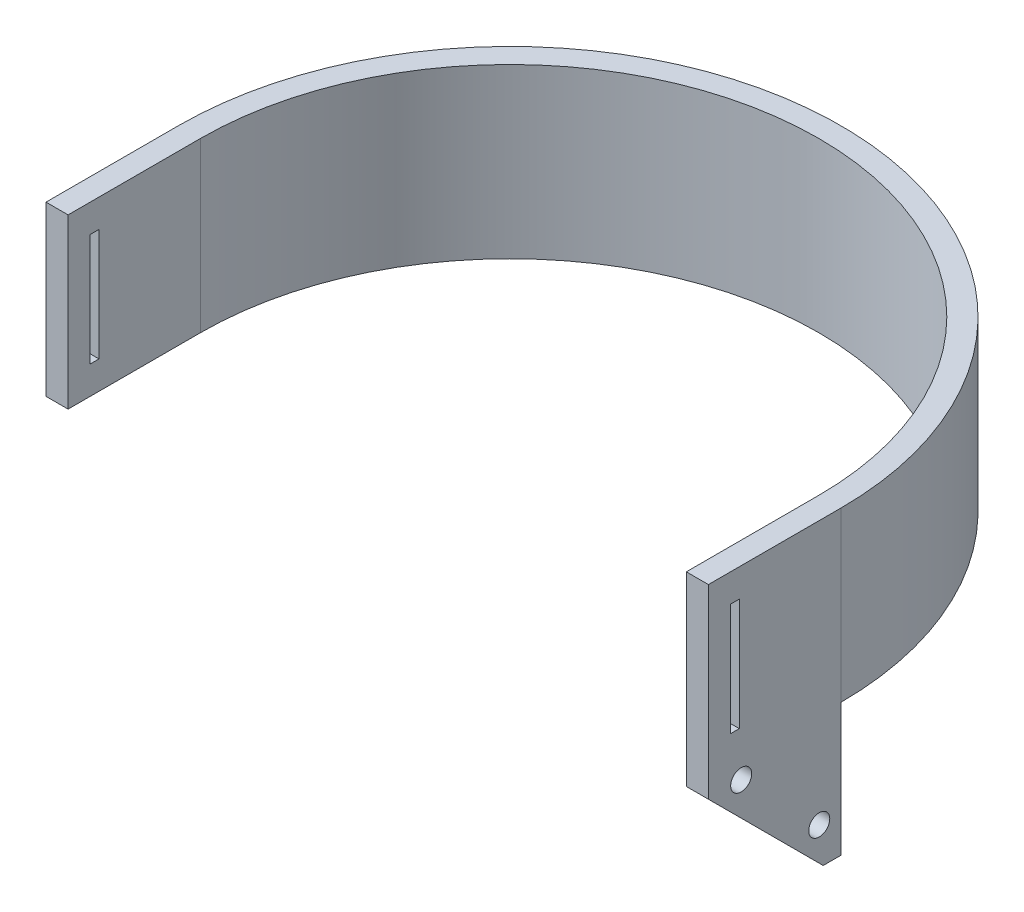
SolidWorks part; units mm, degrees
ref_plane "Front Plane" through (0, 0, 0) normal (0, 0, 1) x (1, 0, 0)
ref_plane "Top Plane" through (0, 0, 0) normal (0, 1, 0) x (1, 0, 0)
ref_plane "Right Plane" through (0, 0, 0) normal (1, 0, 0) x (0, 0, -1)
sketch "Sketch1" plane through (0, 0, 0) normal (0, 1, 0) x (1, 0, 0)
  line L0 (-75, 0) -> (75, 0)
  line L2 (-75, 0) -> (-70, 0)
  line L3 (-75, 0) -> (-75, -30)
  line L4 (-75, -30) -> (-70, -30)
  line L5 (-70, 0) -> (-70, -30)
  line L6 (70, 0) -> (75, 0)
  line L7 (70, 0) -> (70, -30)
  line L8 (70, -30) -> (75, -30)
  line L9 (75, 0) -> (75, -30)
  arc A0 (70, 0) -> (-70, 0) centre (0, 0) ccw
  arc A1 (75, 0) -> (-75, 0) centre (0, 0) ccw
  circle A2 centre (0, 0) radius 70 construction
  circle A3 centre (0, 0) radius 75 construction
  dimension "D1" = 140
  dimension "D3" = 30
  dimension "D2" = 5
extrude "Boss-Extrude1" add sketch "Sketch1" along normal blind 38.1 contours L5 L0 L3 L4 | L0 A1 A0 | L9 L0 L7 L8
sketch "Sketch2" plane through (75, 0, 0) normal (1, 0, 0) x (0, 0, -1)
  line L0 (0, 38.1) -> (-30, 38.1) construction
  line L1 (-25, 31.75) -> (-23, 31.75)
  line L2 (-25, 31.75) -> (-25, 6.35)
  line L3 (-25, 6.35) -> (-23, 6.35)
  line L4 (-23, 31.75) -> (-23, 6.35)
  line L5 (0, 0) -> (-30, 0) construction
  line L6 (-30, 38.1) -> (-30, 0) construction
  dimension "D1" = 6.35
  dimension "D2" = 6.35
  dimension "D3" = 5
  dimension "D4" = 2
extrude "Cut-Extrude1" cut sketch "Sketch2" against normal through all
sketch "Sketch3" plane through (75, 0, 0) normal (1, 0, 0) x (0, 0, -1)
  line L0 (-30, 0) -> (0, -30)
  line L1 (-30, 0) -> (0, 0)
  line L2 (-30, 0) -> (-30, -30)
  line L3 (-30, -30) -> (0, -30)
  line L4 (0, 0) -> (0, -30)
  line L5 (-30, 0) -> (0, -30)
  line L6 (-30, 0) -> (-26.4645, 3.5355)
  line L7 (0, -30) -> (3.5355, -26.4645)
  line L8 (-26.4645, 3.5355) -> (3.5355, -26.4645)
  line L9 (-28.2322, 1.7678) -> (1.7678, -28.2322)
  line L10 (-30, -4) -> (-4, -30)
  circle A0 centre (-22.5754, -3.8891) radius 2.3812
  circle A1 centre (-4.8977, -21.5668) radius 2.3813
  line M14 (-30, 0) -> (0, 0)
  dimension "D3" = 4.7625
  dimension "D6" = 4.7625
  dimension "D1" = 30
  dimension "D2" = 5
  dimension "D4" = 4
  dimension "D5" = 4
  dimension "D7" = 8
  dimension "D8" = 25
extrude "Boss-Extrude2" add sketch "Sketch3" against normal blind 5 contours L2 L10 L3 L0 | A1 L9 A0 L0 L4 M14 | A1 L9 L4 L8 L1 A0 | L1 L8 L4
